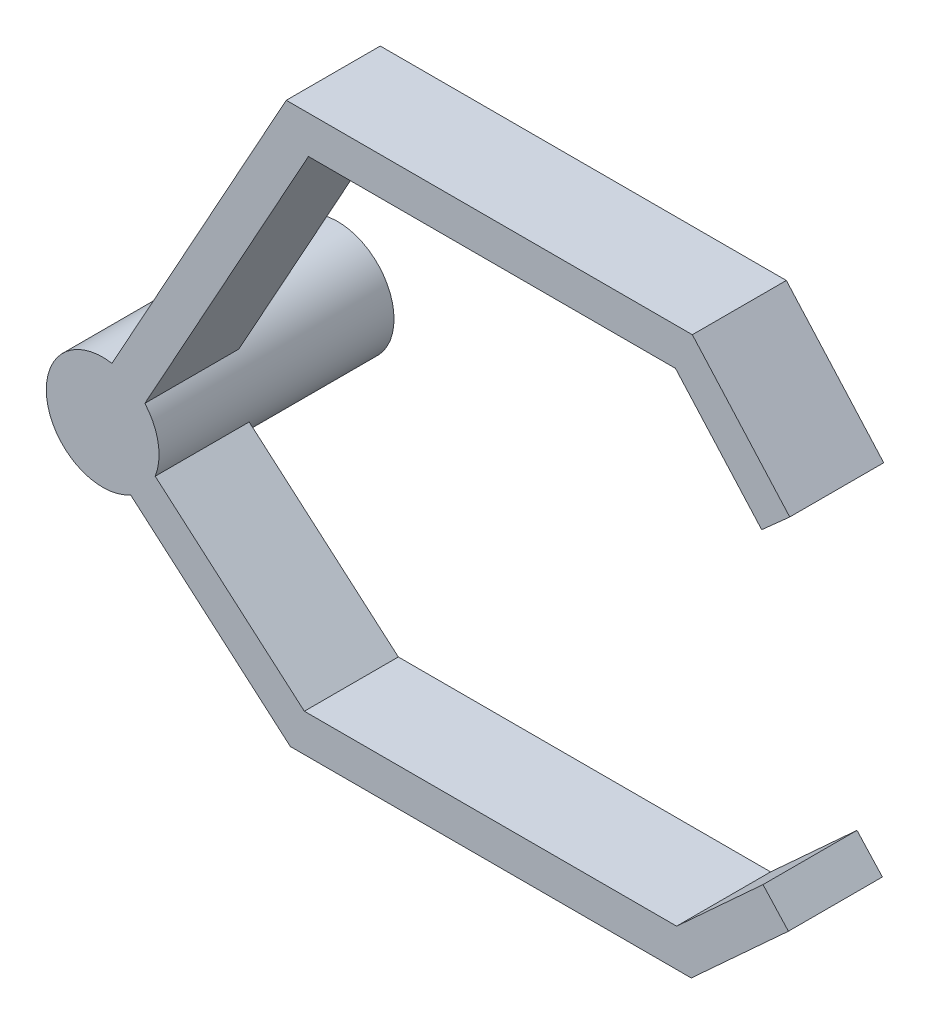
SolidWorks part; units mm, degrees
ref_plane "Front Plane" through (0, 0, 0) normal (0, 0, 1) x (1, 0, 0)
ref_plane "Top Plane" through (0, 0, 0) normal (0, 1, 0) x (1, 0, 0)
ref_plane "Right Plane" through (0, 0, 0) normal (1, 0, 0) x (0, 0, -1)
sketch "Sketch1" plane through (0, 0, 0) normal (0, 0, 1) x (1, 0, 0)
  line L0 (61.8491, -17.9037) -> (71.6147, -8.9518) construction
  line L1 (20.715, -17.9037) -> (61.8491, -17.9037) construction
  line L2 (0, 0) -> (20.715, -17.9037) construction
  line L20 (0, 52.8018) -> (0, -40.6652) construction
  line L21 (61.8491, 37.435) -> (71.6147, 26.4856) construction
  line L22 (20.715, 37.435) -> (61.8491, 37.435) construction
  line L23 (0, 0) -> (20.715, 37.435) construction
  line L24 (73.1073, 27.8168) -> (70.1221, 25.1544)
  line L25 (60.953, 35.435) -> (70.1221, 25.1544)
  line L26 (21.8941, 35.435) -> (60.953, 35.435)
  line L27 (2.5358, 0.4518) -> (21.8941, 35.435)
  line L28 (62.7452, 39.435) -> (73.1073, 27.8168)
  line L29 (19.5359, 39.435) -> (62.7452, 39.435)
  line L30 (-2.5358, -0.4518) -> (19.5359, 39.435)
  line L40 (70.2633, -7.4775) -> (72.9662, -10.4261)
  line L41 (2.5358, 0.4518) -> (21.4595, -15.9037)
  line L42 (21.4595, -15.9037) -> (61.0711, -15.9037)
  line L43 (61.0711, -15.9037) -> (70.2633, -7.4775)
  line L44 (-2.5358, -0.4518) -> (19.9705, -19.9037)
  line L45 (19.9705, -19.9037) -> (62.627, -19.9037)
  line L46 (62.627, -19.9037) -> (72.9662, -10.4261)
  circle A0 centre (0, 0) radius 6
  dimension "D1" = 12
extrude "Boss-Extrude1" add sketch "Sketch1" along normal blind 10 contours A0 L27 L26 L25 L24 L28 L29 L30 | L41 A0 L27 | L30 A0 L44 | A0 L44 L45 L46 L40 L43 L42 L41
sketch "Sketch2" plane through (0, 0, 10) normal (0, 0, 1) x (1, 0, 0)
  circle A0 centre (0, 0) radius 6
extrude "Boss-Extrude2" add sketch "Sketch2" against normal blind 25
